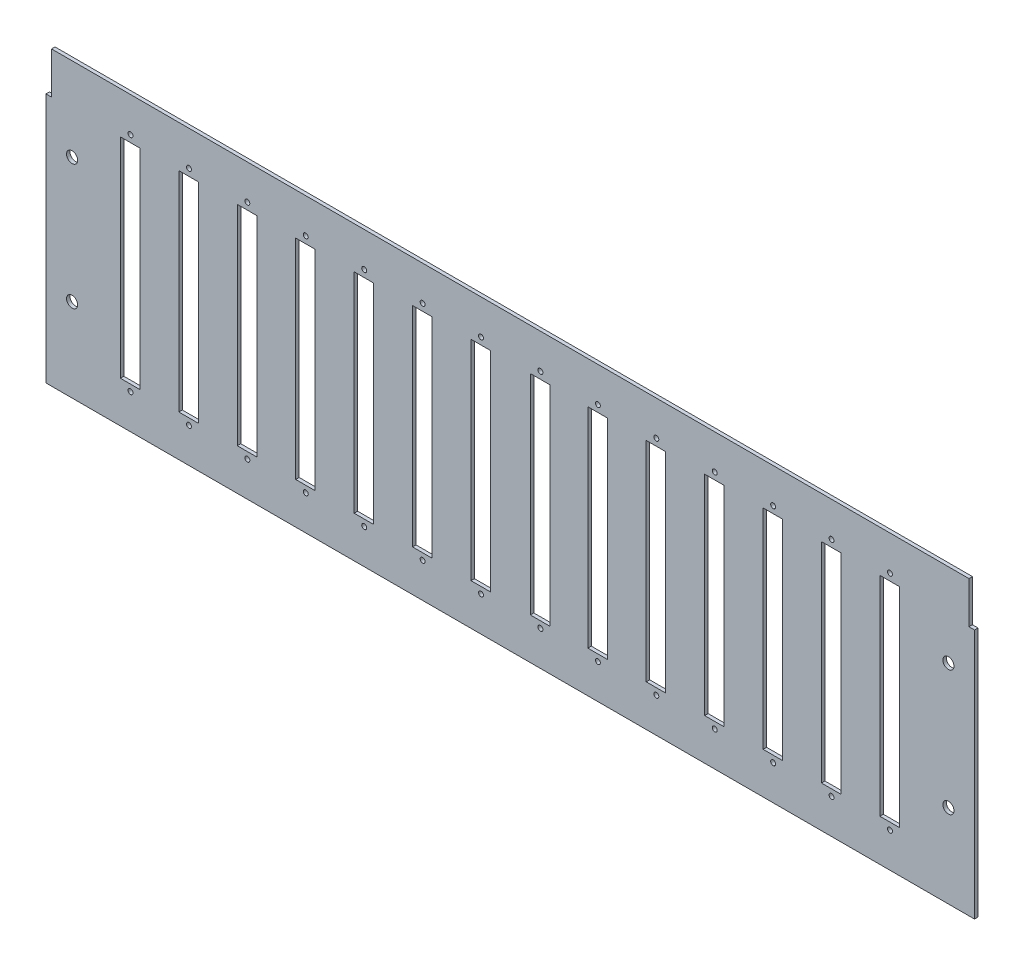
SolidWorks part; units mm, degrees
ref_plane "Front Plane" through (0, 0, 0) normal (0, 0, 1) x (1, 0, 0)
ref_plane "Top Plane" through (0, 0, 0) normal (0, 1, 0) x (1, 0, 0)
ref_plane "Right Plane" through (0, 0, 0) normal (1, 0, 0) x (0, 0, -1)
sketch "Sketch1" plane through (0, 0, 0) normal (0, 0, 1) x (1, 0, 0)
  line L0 (0, 0) -> (0, 114.3)
  line L5 (0, 0) -> (423.8752, 0)
  line L7 (2.54, 133.35) -> (421.3352, 133.35)
  line L9 (33.9788, 114.3) -> (42.8688, 114.3)
  line L10 (33.9788, 114.3) -> (33.9788, 18.8595)
  line L11 (33.9788, 18.8595) -> (42.8688, 18.8595)
  line L12 (42.8688, 114.3) -> (42.8688, 18.8595)
  line L13 (423.8752, 0) -> (423.8752, 114.3)
  line L30 (60.6488, 114.3) -> (69.5388, 114.3)
  line L31 (60.6488, 114.3) -> (60.6488, 18.8595)
  line L32 (60.6488, 18.8595) -> (69.5388, 18.8595)
  line L33 (69.5388, 114.3) -> (69.5388, 18.8595)
  line L34 (87.3188, 114.3) -> (96.2088, 114.3)
  line L35 (87.3188, 114.3) -> (87.3188, 18.8595)
  line L36 (87.3188, 18.8595) -> (96.2088, 18.8595)
  line L37 (96.2088, 114.3) -> (96.2088, 18.8595)
  line L38 (113.9888, 114.3) -> (122.8788, 114.3)
  line L39 (113.9888, 114.3) -> (113.9888, 18.8595)
  line L40 (113.9888, 18.8595) -> (122.8788, 18.8595)
  line L41 (122.8788, 114.3) -> (122.8788, 18.8595)
  line L42 (140.6588, 114.3) -> (149.5488, 114.3)
  line L43 (140.6588, 114.3) -> (140.6589, 18.8595)
  line L44 (140.6589, 18.8595) -> (149.5488, 18.8595)
  line L45 (149.5488, 114.3) -> (149.5488, 18.8595)
  line L46 (247.3389, 114.3) -> (256.2289, 114.3)
  line L47 (247.3389, 114.3) -> (247.3389, 18.8595)
  line L48 (247.3389, 18.8595) -> (256.2289, 18.8595)
  line L49 (256.2289, 114.3) -> (256.2289, 18.8595)
  line L50 (167.3288, 114.3) -> (176.2188, 114.3)
  line L51 (167.3288, 114.3) -> (167.3288, 18.8595)
  line L52 (167.3288, 18.8595) -> (176.2188, 18.8595)
  line L53 (176.2188, 114.3) -> (176.2188, 18.8595)
  line L54 (193.9988, 114.3) -> (202.8888, 114.3)
  line L55 (193.9988, 114.3) -> (193.9989, 18.8595)
  line L56 (193.9989, 18.8595) -> (202.8888, 18.8595)
  line L57 (202.8888, 114.3) -> (202.8888, 18.8595)
  line L58 (221.1004, 114.3) -> (229.9904, 114.3)
  line L59 (221.1004, 114.3) -> (221.1004, 18.8595)
  line L60 (221.1004, 18.8595) -> (229.9904, 18.8595)
  line L61 (229.9904, 114.3) -> (229.9904, 18.8595)
  line L62 (274.0088, 114.3) -> (282.8988, 114.3)
  line L63 (274.0088, 114.3) -> (274.0088, 18.8595)
  line L64 (274.0088, 18.8595) -> (282.8988, 18.8595)
  line L65 (282.8988, 114.3) -> (282.8988, 18.8595)
  line L66 (300.6788, 114.3) -> (309.5688, 114.3)
  line L67 (300.6788, 114.3) -> (300.6788, 18.8595)
  line L92 (300.6788, 18.8595) -> (309.5688, 18.8595)
  line L93 (309.5688, 114.3) -> (309.5688, 18.8595)
  line L94 (327.3488, 114.3) -> (336.2388, 114.3)
  line L95 (327.3488, 114.3) -> (327.3488, 18.8595)
  line L96 (327.3488, 18.8595) -> (336.2388, 18.8595)
  line L97 (336.2388, 114.3) -> (336.2388, 18.8595)
  line L98 (354.0188, 114.3) -> (362.9088, 114.3)
  line L99 (354.0188, 114.3) -> (354.0188, 18.8595)
  line L100 (354.0188, 18.8595) -> (362.9088, 18.8595)
  line L101 (362.9088, 114.3) -> (362.9088, 18.8595)
  line L102 (380.6888, 114.3) -> (389.5788, 114.3)
  line L103 (380.6888, 114.3) -> (380.6888, 19.05)
  line L104 (380.6888, 19.05) -> (389.5788, 19.05)
  line L105 (389.5788, 114.3) -> (389.5788, 19.05)
  line L106 (0, 114.3) -> (2.54, 114.3)
  line L107 (2.54, 114.3) -> (2.54, 133.35)
  line L110 (423.8752, 114.3) -> (421.3352, 114.3)
  line L111 (421.3352, 114.3) -> (421.3352, 133.35)
  circle A0 centre (11.9126, 38.1) radius 2.54
  circle A1 centre (11.9126, 95.25) radius 2.54
  circle A2 centre (411.9626, 95.25) radius 2.54
  circle A3 centre (411.9626, 38.1) radius 2.54
  circle A4 centre (38.5826, 117.475) radius 1.1303
  circle A5 centre (38.5826, 15.875) radius 1.1303
  circle A6 centre (65.2526, 117.475) radius 1.1303
  circle A7 centre (65.2526, 15.875) radius 1.1303
  circle A8 centre (91.9226, 117.475) radius 1.1303
  circle A9 centre (91.9226, 15.875) radius 1.1303
  circle A10 centre (118.5926, 117.475) radius 1.1303
  circle A11 centre (118.5926, 15.875) radius 1.1303
  circle A12 centre (145.2626, 117.475) radius 1.1303
  circle A13 centre (145.2626, 15.875) radius 1.1303
  circle A14 centre (171.9326, 117.475) radius 1.1303
  circle A15 centre (171.9326, 15.875) radius 1.1303
  circle A16 centre (198.6026, 117.475) radius 1.1303
  circle A17 centre (198.6026, 15.875) radius 1.1303
  circle A18 centre (225.7042, 117.475) radius 1.1303
  circle A19 centre (225.7042, 15.875) radius 1.1303
  circle A32 centre (251.9426, 117.475) radius 1.1303
  circle A33 centre (251.9426, 15.875) radius 1.1303
  circle A34 centre (278.6126, 117.475) radius 1.1303
  circle A35 centre (278.6126, 15.875) radius 1.1303
  circle A36 centre (305.2826, 117.475) radius 1.1303
  circle A37 centre (305.2826, 15.875) radius 1.1303
  circle A38 centre (331.9526, 117.475) radius 1.1303
  circle A39 centre (331.9526, 15.875) radius 1.1303
  circle A40 centre (358.6226, 117.475) radius 1.1303
  circle A41 centre (358.6226, 15.875) radius 1.1303
  circle A42 centre (385.2926, 117.475) radius 1.1303
  circle A43 centre (385.2926, 15.875) radius 1.1303
  point P3 (0, 0)
  point P21 (0, 0)
  dimension "D3" = 400.05
  dimension "D7" = 38.5826
  dimension "D8" = 8.89
  dimension "D13" = 5.08
  dimension "D14" = 26.67
  dimension "D30" = 2.2606
  dimension "D9" = 5.08
  dimension "D2" = 2.54
  dimension "D4" = 11.9126
  dimension "D5" = 33.9788
  dimension "D6" = 26.67
  dimension "D10" = 57.15
  dimension "D11" = 38.1
  dimension "D12" = 133.35
  dimension "D15" = 95.25
  dimension "D16" = 8.89
  dimension "D17" = 19.05
  dimension "D18" = 8.89
  dimension "D19" = 8.89
  dimension "D20" = 8.89
  dimension "D21" = 8.89
  dimension "D22" = 8.89
  dimension "D23" = 8.89
  dimension "D24" = 8.89
  dimension "D25" = 8.89
  dimension "D26" = 8.89
  dimension "D27" = 8.89
  dimension "D28" = 8.89
  dimension "D29" = 8.89
  dimension "D31" = 423.8752
  dimension "D32" = 101.6
extrude "Boss-Extrude1" add sketch "Sketch1" along normal blind 1.5875
